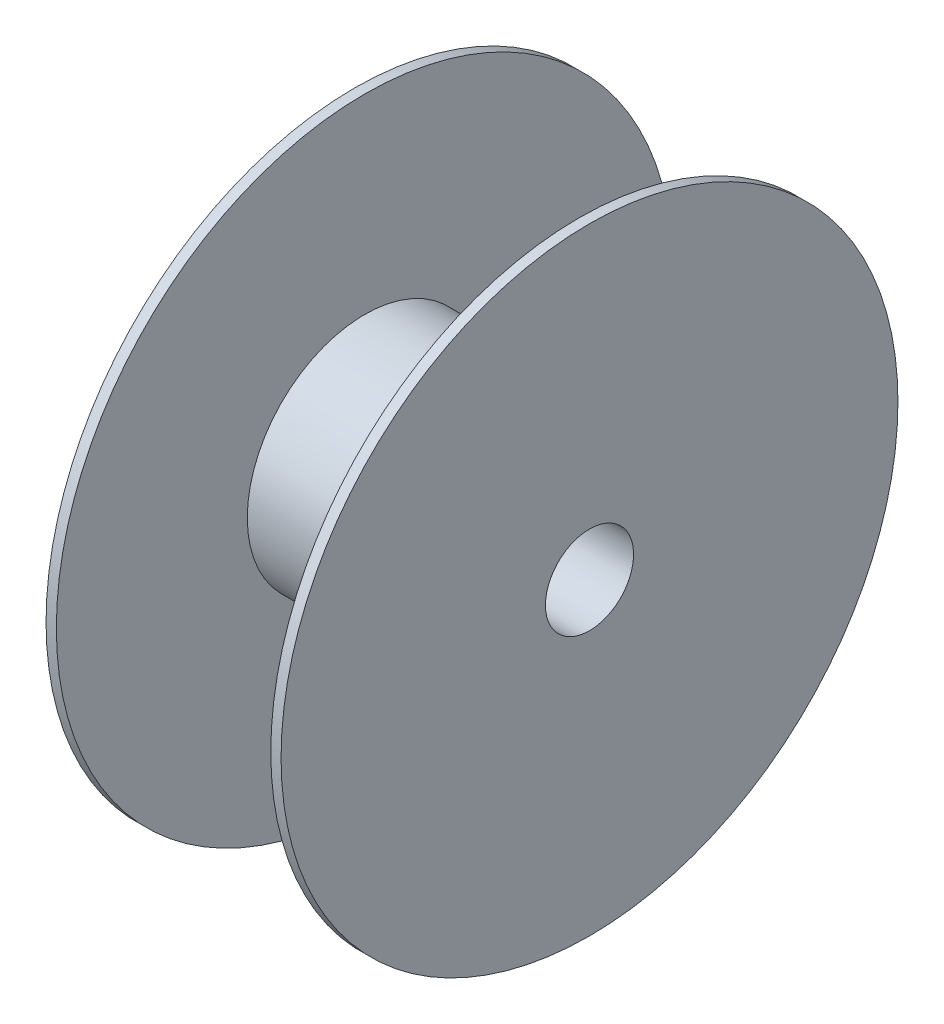
SolidWorks part; units mm, degrees
ref_plane "Front Plane" through (0, 0, 0) normal (0, 0, 1) x (1, 0, 0)
ref_plane "Top Plane" through (0, 0, 0) normal (0, 1, 0) x (1, 0, 0)
ref_plane "Right Plane" through (0, 0, 0) normal (1, 0, 0) x (0, 0, -1)
sketch "Sketch1" plane through (0, 0, 0) normal (0, 0, 1) x (1, 0, 0)
  line L0 (0, 0) -> (52.484, 0) construction
  line L1 (101.6, 19.05) -> (0, 19.05)
  line L4 (0, 19.05) -> (0, 133.35)
  line L5 (0, 133.35) -> (4.445, 133.35)
  line L6 (4.445, 133.35) -> (4.445, 50.8)
  line L7 (4.445, 50.8) -> (97.155, 50.8)
  line L8 (97.155, 50.8) -> (97.155, 133.35)
  line L9 (97.155, 133.35) -> (101.6, 133.35)
  line L10 (101.6, 133.35) -> (101.6, 19.05)
  dimension "D1" = 4.445
  dimension "D2" = 101.6
  dimension "D4" = 38.1
  dimension "D5" = 101.6
  dimension "D6" = 266.7
revolve "Revolve1" add sketch "Sketch1" angle 360 about L0
